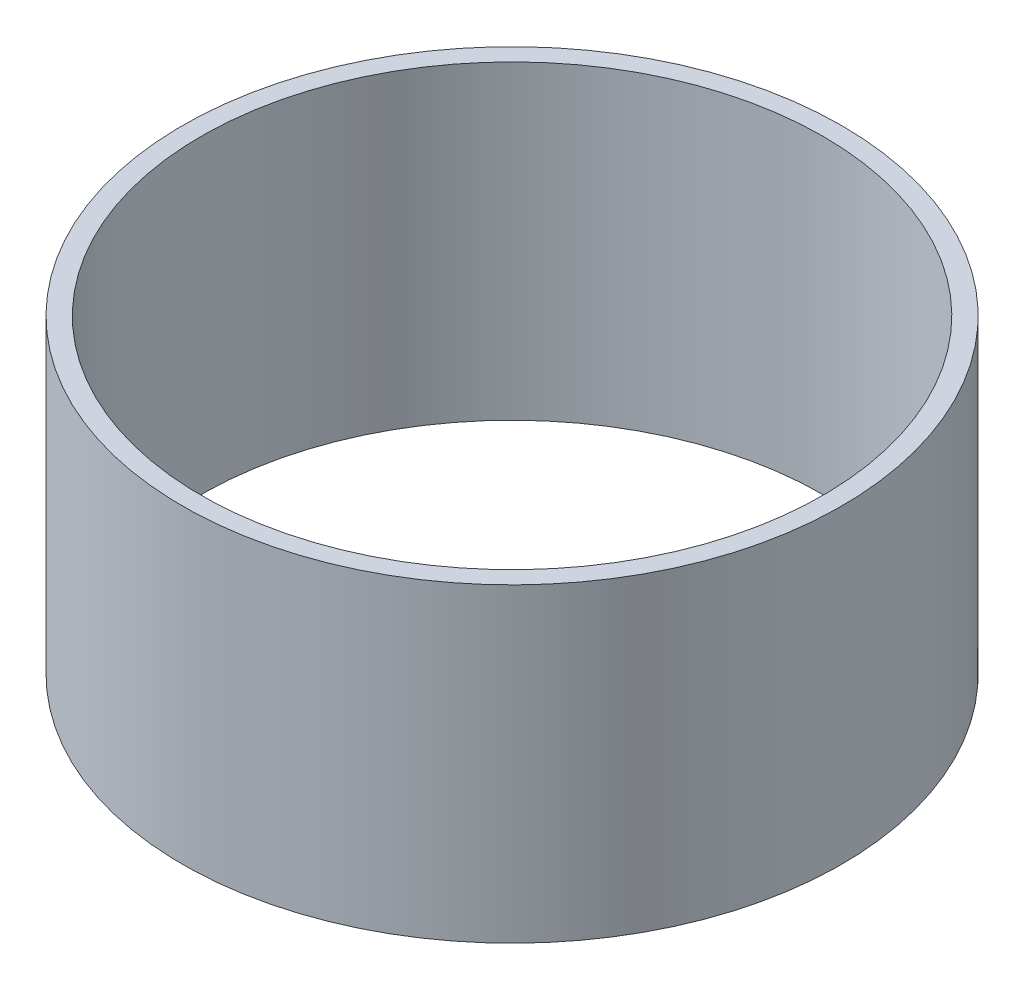
SolidWorks part; units mm, degrees
ref_plane "Front Plane" through (0, 0, 0) normal (0, 0, 1) x (1, 0, 0)
ref_plane "Top Plane" through (0, 0, 0) normal (0, 1, 0) x (1, 0, 0)
ref_plane "Right Plane" through (0, 0, 0) normal (1, 0, 0) x (0, 0, -1)
sketch "Sketch1" plane through (0, 0, 0) normal (0, 0, 1) x (1, 0, 0)
  line L1 (25.4508, 0) -> (26.9748, 0)
  line L2 (25.4508, 0) -> (25.4508, 25.4)
  line L3 (25.4508, 25.4) -> (26.9748, 25.4)
  line L4 (26.9748, 0) -> (26.9748, 25.4)
  dimension "D1" = 26.9748
  dimension "D2" = 1.524
  dimension "D3" = 25.4
  dimension "D4" = 0
ref_axis "Axis1" through (0, -13.97, 0) along (0, 1, 0)
revolve "Revolve1" add sketch "Sketch1" angle 360 about axis through (0, -13.97, 0) along (0, 1, 0)
